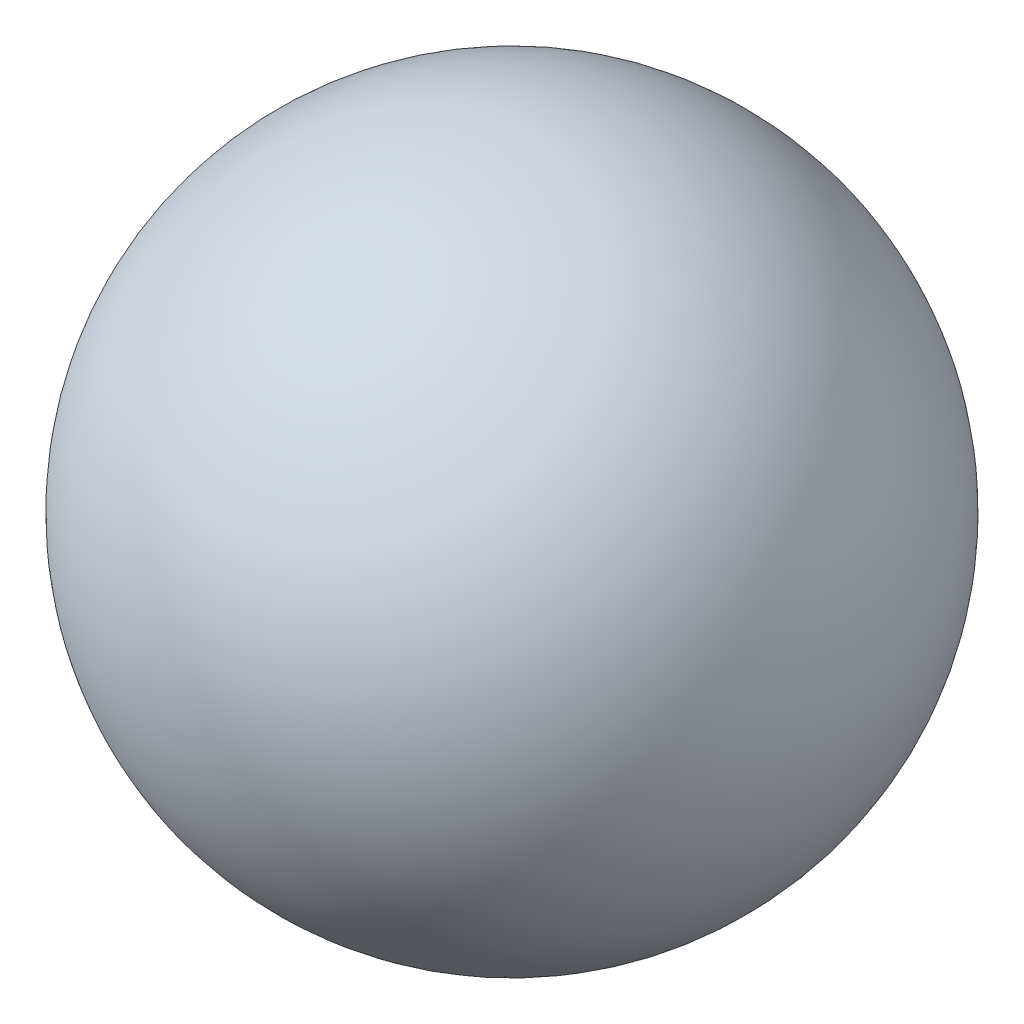
SolidWorks part; units mm, degrees
material "AISI 316 Barra de acero inoxidable recocido (SS)"
ref_plane "Alzado" through (0, 0, 0) normal (0, 0, 1) x (1, 0, 0)
ref_plane "Planta" through (0, 0, 0) normal (0, 1, 0) x (1, 0, 0)
ref_plane "Vista lateral" through (0, 0, 0) normal (1, 0, 0) x (0, 0, -1)
sketch "Croquis1" plane through (0, 0, 0) normal (0, 1, 0) x (1, 0, 0)
  line L0 (0, 4.75) -> (0, -4.75) construction
  line L1 (0, 4.75) -> (0, -4.75)
  arc A0 (0, -4.75) -> (0, 4.75) centre (0, 0) ccw
  dimension "D1" = 9.5
revolve "Revolución5" add sketch "Croquis1" angle 360 about L0
